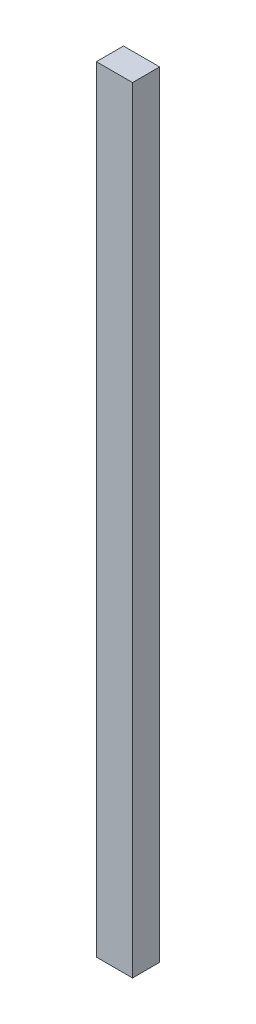
SolidWorks part; units mm, degrees
ref_plane "Front Plane" through (0, 0, 0) normal (0, 0, 1) x (1, 0, 0)
ref_plane "Top Plane" through (0, 0, 0) normal (0, 1, 0) x (1, 0, 0)
ref_plane "Right Plane" through (0, 0, 0) normal (1, 0, 0) x (0, 0, -1)
sketch "Sketch1" plane through (0, 0, 0) normal (0, 1, 0) x (1, 0, 0)
  line L1 (0, 0) -> (25.4, 0)
  line L2 (0, 0) -> (0, 19.05)
  line L3 (0, 19.05) -> (25.4, 19.05)
  line L4 (25.4, 0) -> (25.4, 19.05)
  dimension "D1" = 19.05
  dimension "D2" = 25.4
extrude "Boss-Extrude1" add sketch "Sketch1" along normal blind 544.576
